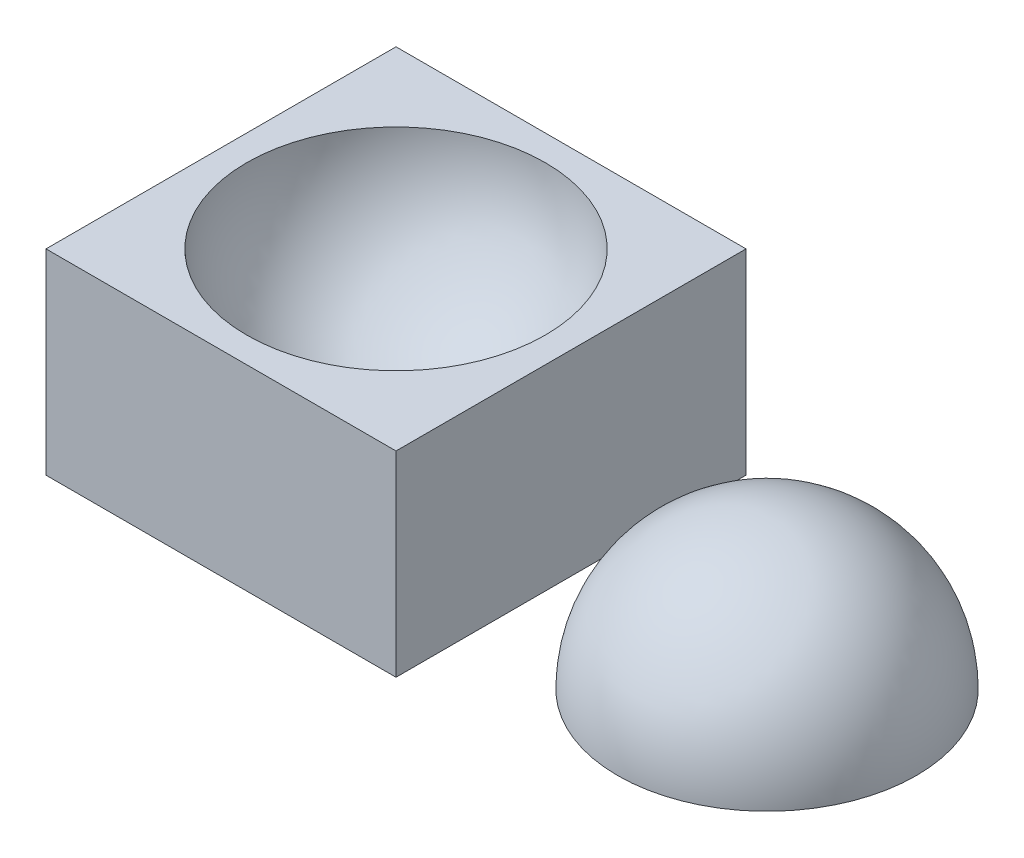
SolidWorks part; units mm, degrees
ref_plane "Front" through (0, 0, 0) normal (0, 0, 1) x (1, 0, 0)
ref_plane "Top" through (0, 0, 0) normal (0, 1, 0) x (1, 0, 0)
ref_plane "Right" through (0, 0, 0) normal (1, 0, 0) x (0, 0, -1)
sketch "Sketch2" plane through (0, 0, 0) normal (0, 1, 0) x (1, 0, 0)
  line L0 (-37.5, 0) -> (37.5, 0) construction
  line L1 (-37.5, -37.5) -> (37.5, -37.5)
  line L2 (-37.5, -37.5) -> (-37.5, 37.5)
  line L3 (-37.5, 37.5) -> (37.5, 37.5)
  line L4 (37.5, -37.5) -> (37.5, 37.5)
  dimension "D1" = 75
  dimension "D2" = 75
extrude "Boss-Extrude2" add sketch "Sketch2" along normal blind 42
sketch "Sketch4" plane through (0, 0, 0) normal (1, 0, 0) x (0, 0, -1)
  line L0 (0, 42) -> (0, 10)
  line L1 (-37.5, 42) -> (37.5, 42) construction
  line L2 (0, 42) -> (32, 42)
  arc A0 (0, 10) -> (32, 42) centre (0, 42) ccw
  dimension "D1" = 32
revolve "Cut-Revolve2" cut sketch "Sketch4" angle 360 about L0
sketch "Sketch5" plane through (0, 0, 0) normal (0, 1, 0) x (1, 0, 0)
  line L0 (37.5, 0) -> (47.5, 0) construction
  line L1 (37.5, -37.5) -> (37.5, 37.5) construction
  dimension "D1" = 10
sketch "Sketch6" plane through (0, 0, 0) normal (0, 0, 1) x (1, 0, 0)
  line L0 (47.5, 0) -> (79.5, 0) construction
  line L1 (37.5, 0) -> (47.5, 0) construction
  line L2 (79.5, 0) -> (79.5, 32) construction
  line L3 (47.5, 0) -> (79.5, 0)
  line L4 (79.5, 0) -> (79.5, 32)
  arc A0 (47.5, 0) -> (79.5, 32) centre (79.5, 0) cw
  dimension "D1" = 32
  dimension "D2" = 32
revolve "Revolve1" add sketch "Sketch6" angle 360 about L4
